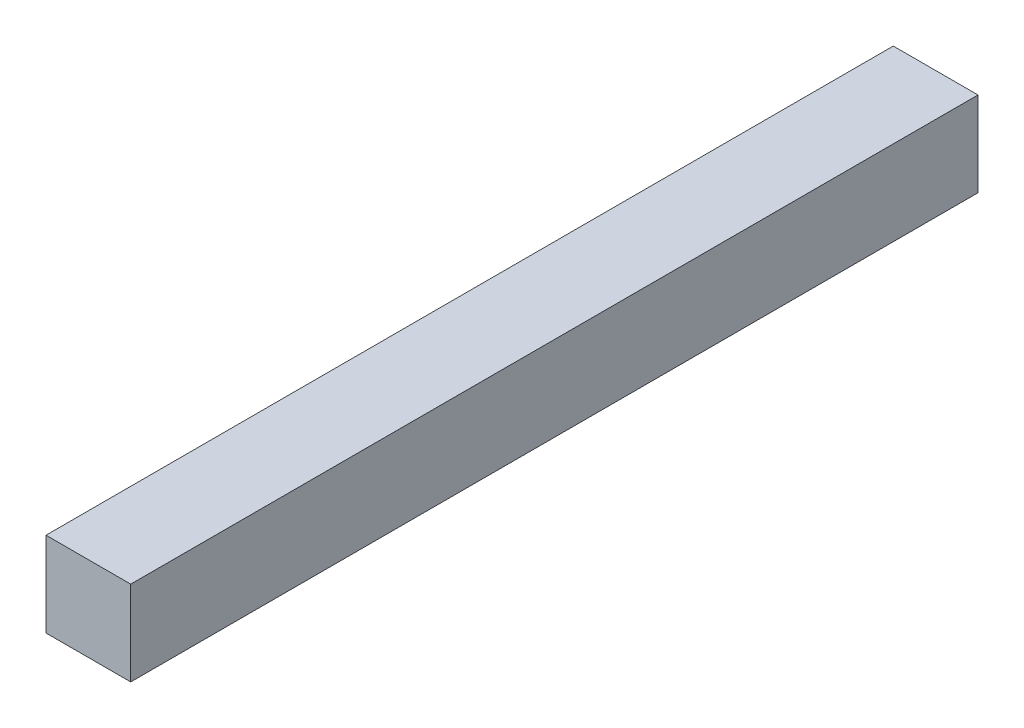
SolidWorks part; units mm, degrees
ref_plane "Front Plane" through (0, 0, 0) normal (0, 0, 1) x (1, 0, 0)
ref_plane "Top Plane" through (0, 0, 0) normal (0, 1, 0) x (1, 0, 0)
ref_plane "Right Plane" through (0, 0, 0) normal (1, 0, 0) x (0, 0, -1)
sketch "Sketch1" plane through (0, 0, 0) normal (0, 0, 1) x (1, 0, 0)
  line L5 (0, 0) -> (10, 0)
  line L6 (0, 0) -> (0, -10)
  line L7 (0, -10) -> (10, -10)
  line L8 (10, 0) -> (10, -10)
  dimension "D1" = 10
  dimension "D2" = 10
extrude "Boss-Extrude1" add sketch "Sketch1" along normal blind 205
sketch "Sketch2" plane through (10, 0, 0) normal (1, 0, 0) x (0, 0, -1)
  line L0 (-205, -10) -> (-205, 0) construction
  circle A2 centre (-200, -5.054) radius 3.5
  dimension "D2" = 7
  dimension "D1" = 5
extrude "Boss-Extrude2" add sketch "Sketch2" along normal blind 8
sketch "Sketch4" plane through (0, 0, 205) normal (0, 0, 1) x (1, 0, 0)
  line L1 (0, -10) -> (18.7666, -10)
  line L2 (0, -10) -> (0, 0.4994)
  line L3 (0, 0.4994) -> (18.7666, 0.4994)
  line L4 (18.7666, -10) -> (18.7666, 0.4994)
extrude "Cut-Extrude1" cut sketch "Sketch4" against normal blind 105
